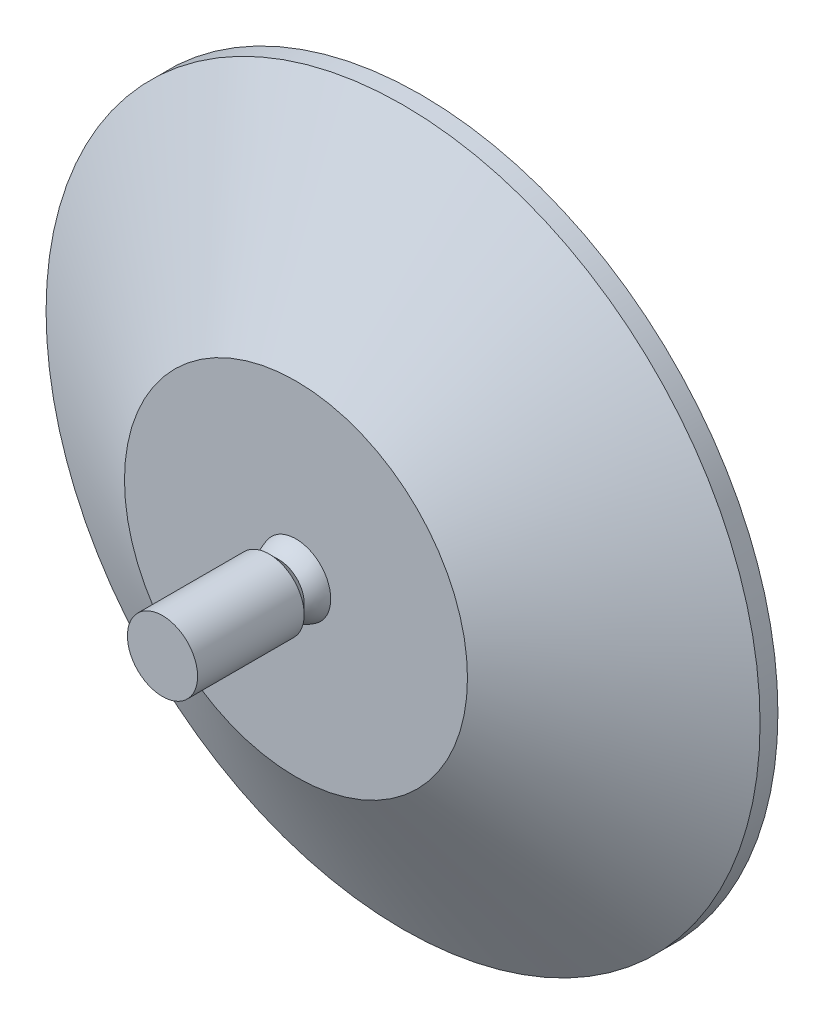
SolidWorks part; units mm, degrees
ref_plane "Plan de face" through (0, 0, 0) normal (0, 0, 1) x (1, 0, 0)
ref_plane "Plan de dessus" through (0, 0, 0) normal (0, 1, 0) x (1, 0, 0)
ref_plane "Plan de droite" through (0, 0, 0) normal (1, 0, 0) x (0, 0, -1)
sketch "Esquisse1" plane through (0, 0, 0) normal (0, 0, 1) x (1, 0, 0)
  circle A0 centre (0, 0) radius 40
  dimension "D1" = 80
extrude "Boss.-Extru.1" add sketch "Esquisse1" along normal blind 2
sketch "Esquisse2" plane through (0, 0, 2) normal (0, 0, 1) x (1, 0, 0)
  circle A1 centre (0, 0) radius 40
  circle A2 centre (0, 0) radius 40
  dimension "D1" = 0
extrude "Boss.-Extru.2" add sketch "Esquisse2" along normal blind 12 draft 60
sketch "Esquisse3" plane through (0, 0, 0) normal (0, 1, 0) x (1, 0, 0)
  line L0 (2.8284, -15.9073) -> (3.932, -17.0109)
  line L1 (3.932, -17.0109) -> (3.932, -28.9558)
  line L2 (3.932, -28.9558) -> (0, -28.9558)
  line L4 (0, -9.0789) -> (0, -28.9558) construction
  line L5 (0, -28.9558) -> (0, -9.0789)
  arc A0 (2.8284, -15.9073) -> (0, -9.0789) centre (0, -13.0789) ccw
  dimension "D1" = 8
revolve "Révolution1" add sketch "Esquisse3" angle 360 about L5
